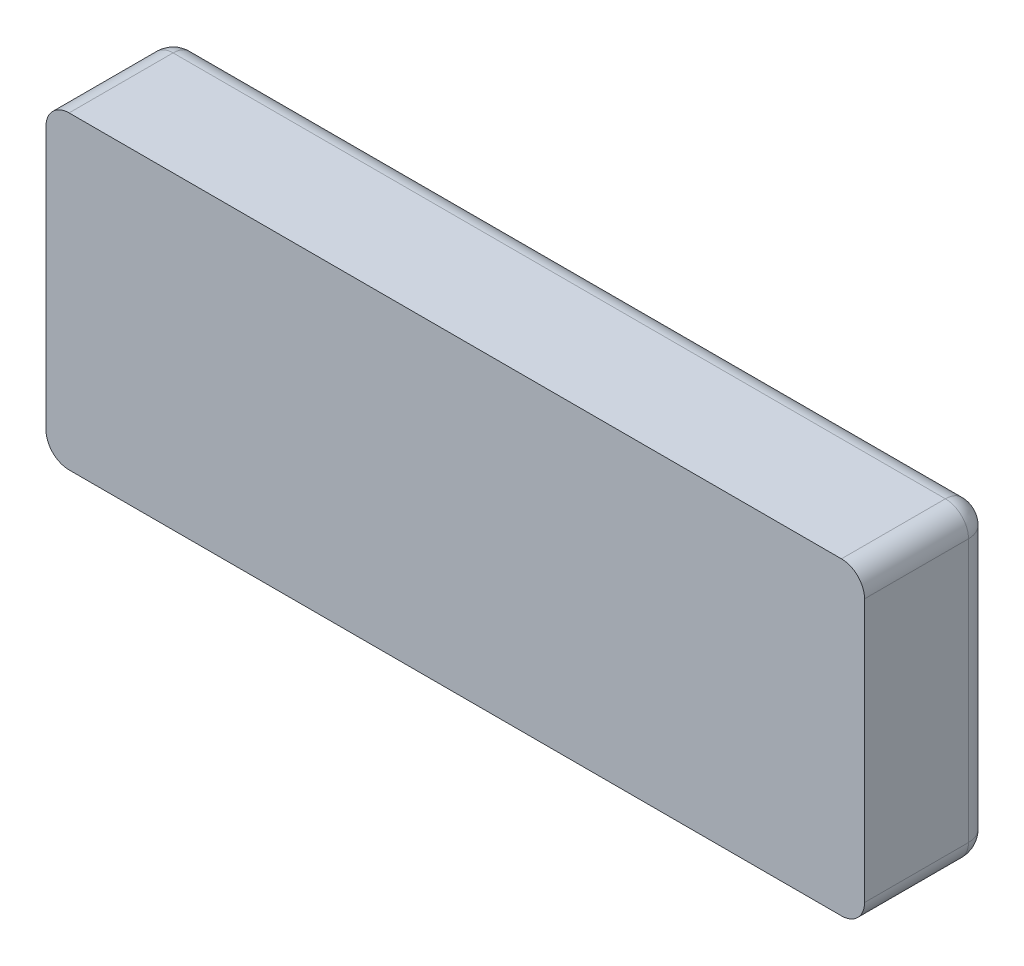
SolidWorks part; units mm, degrees
ref_plane "Front Plane" through (0, 0, 0) normal (0, 0, 1) x (1, 0, 0)
ref_plane "Top Plane" through (0, 0, 0) normal (0, 1, 0) x (1, 0, 0)
ref_plane "Right Plane" through (0, 0, 0) normal (1, 0, 0) x (0, 0, -1)
sketch "Sketch1" plane through (0, 0, 0) normal (0, 0, 1) x (1, 0, 0)
  line L1 (-45, -17) -> (45, -17)
  line L2 (-45, -17) -> (-45, 17)
  line L3 (-45, 17) -> (45, 17)
  line L4 (45, -17) -> (45, 17)
  line L5 (-45, -17) -> (45, 17) construction
  line L6 (-45, 17) -> (45, -17) construction
  point P0 (0, 0)
  dimension "D1" = 90
  dimension "D2" = 34
extrude "Boss-Extrude1" add sketch "Sketch1" along normal blind 13.97
fillet "Fillet1" radius 2.54 8 edges at (0, 17, 0) (-45, 0, 0) (0, -17, 0) (45, 0, 0) (-45, 17, 6.985) (-45, -17, 6.985) (45, -17, 6.985) (45, 17, 6.985)
